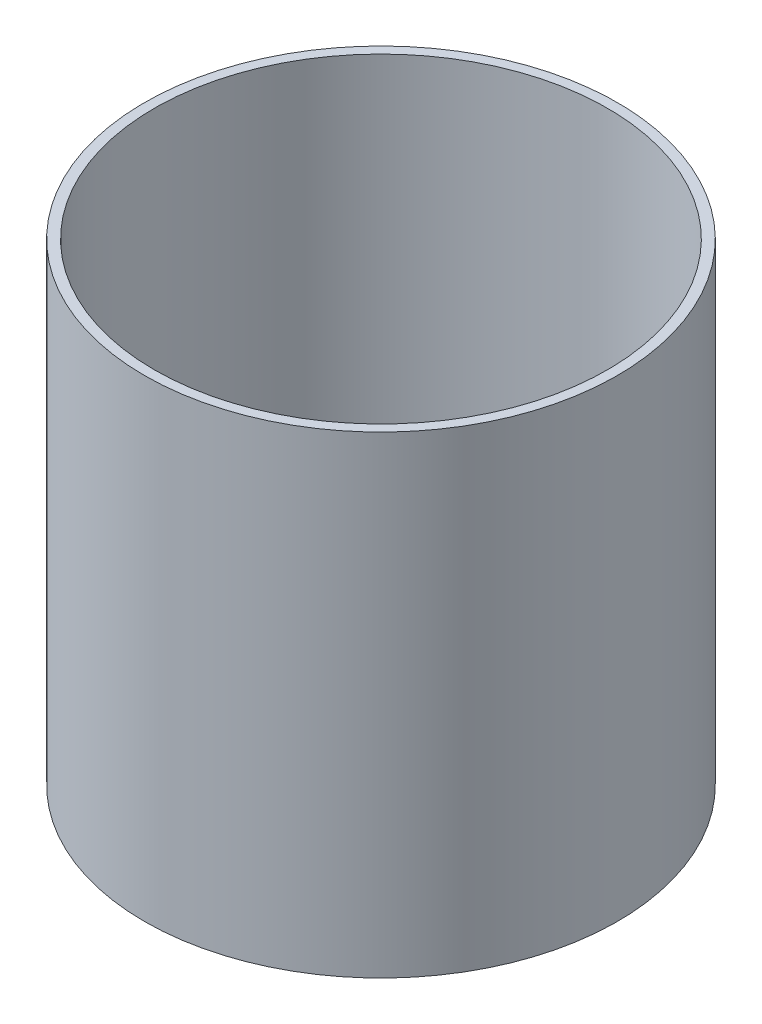
SolidWorks part; units mm, degrees
material "6061-T6"
ref_plane "Front Plane" through (0, 0, 0) normal (0, 0, 1) x (1, 0, 0)
ref_plane "Top Plane" through (0, 0, 0) normal (0, 1, 0) x (1, 0, 0)
ref_plane "Right Plane" through (0, 0, 0) normal (1, 0, 0) x (0, 0, -1)
sketch "Sketch1" plane through (0, 0, 0) normal (0, 1, 0) x (1, 0, 0)
  circle A0 centre (0, 0) radius 152.4
  circle A1 centre (0, 0) radius 146.05
  dimension "D1" = 304.8
  dimension "D2" = 6.35
extrude "Boss-Extrude1" add sketch "Sketch1" along normal blind 304.8
